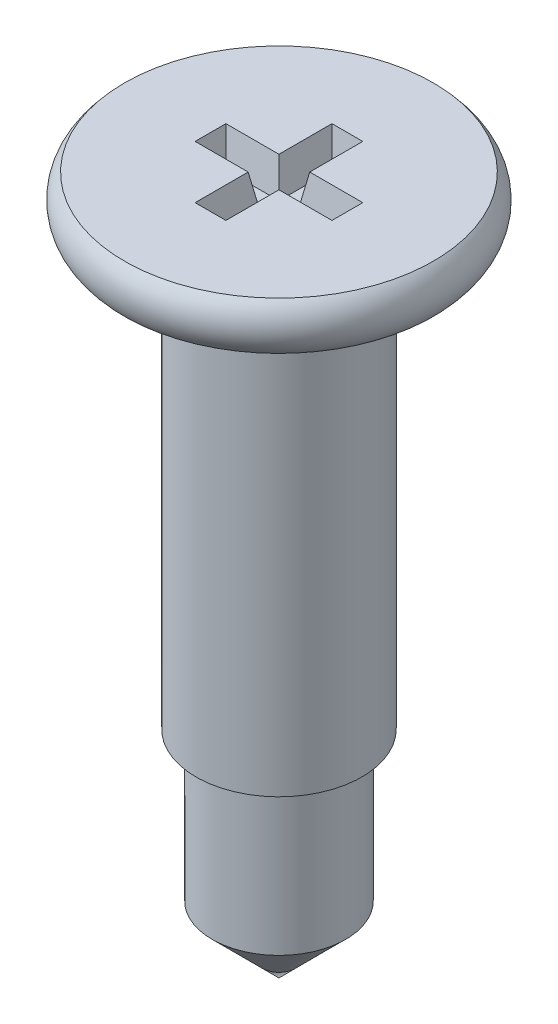
SolidWorks part; units mm, degrees
material "Plain Carbon Steel"
ref_plane "Front Plane" through (0, 0, 0) normal (0, 0, 1) x (1, 0, 0)
ref_plane "Top Plane" through (0, 0, 0) normal (0, 1, 0) x (1, 0, 0)
ref_plane "Right Plane" through (0, 0, 0) normal (1, 0, 0) x (0, 0, -1)
sketch "Sketch2" plane through (0, 0, 0) normal (0, 0, 1) x (1, 0, 0)
  line L0 (-2.425, 0) -> (-2.425, -12.7)
  line L2 (-2.425, -12.7) -> (-1.95, -12.7)
  line L3 (-1.95, -12.7) -> (-1.95, -17.05)
  line L4 (-1.95, -17.05) -> (0, -19)
  line L5 (0, -19) -> (0, 0)
  line L6 (-2.425, 0) -> (-4.5141, 0)
  line L7 (0, -19) -> (0, -22.7626) construction
  line L8 (-4.5141, 1.4) -> (0, 1.4)
  line L9 (0, 1.4) -> (0, 0)
  line L10 (-3.8, 0.7) -> (0, 0.7) construction
  arc A0 (-4.5141, 0) -> (-4.5141, 1.4) centre (-3.8, 0.7) cw
  dimension "D7" = 9.6
  dimension "D8" = 1
  dimension "D1" = 4.85
  dimension "D2" = 3.9
  dimension "D3" = 19
  dimension "D4" = 45
  dimension "D5" = 12.7
  dimension "D6" = 1.4
revolve "Revolve1" add sketch "Sketch2" angle 360 about L7
sketch "Sketch3" plane through (0, 1.4, 0) normal (0, 1, 0) x (1, 0, 0)
  line L0 (-0.45, 2) -> (-0.45, 0.45)
  line L1 (-0.45, 0.45) -> (-2, 0.45)
  line L2 (-1.0057, 0) -> (0, 0) construction
  line L3 (0, 0) -> (0, 1.2021) construction
  line L4 (0.45, 0.45) -> (2, 0.45)
  line L5 (0.45, 2) -> (0.45, 0.45)
  line L6 (0.45, -2) -> (0.45, -0.45)
  line L7 (0.45, -0.45) -> (2, -0.45)
  line L8 (-0.45, -0.45) -> (-2, -0.45)
  line L9 (-0.45, -2) -> (-0.45, -0.45)
  line L10 (-0.45, 2) -> (0.45, 2)
  line L11 (-2, -0.45) -> (-2, 0.45)
  line L12 (-0.45, -2) -> (0.45, -2)
  line L13 (2, -0.45) -> (2, 0.45)
  dimension "D1" = 0.9
  dimension "D2" = 4
extrude "Cut-Extrude1" cut sketch "Sketch3" against normal blind 1 draft 10
